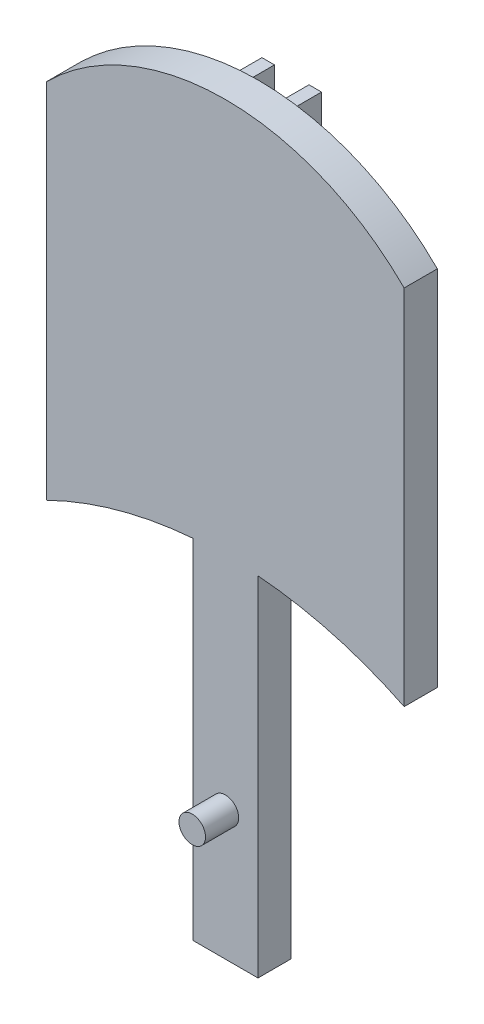
SolidWorks part; units mm, degrees
ref_plane "Front Plane" through (0, 0, 0) normal (0, 0, 1) x (1, 0, 0)
ref_plane "Top Plane" through (0, 0, 0) normal (0, 1, 0) x (1, 0, 0)
ref_plane "Right Plane" through (0, 0, 0) normal (1, 0, 0) x (0, 0, -1)
sketch "Sketch1" plane through (0, 0, 0) normal (0, 0, 1) x (1, 0, 0)
  line L1 (-17.1143, -17.3576) -> (17.1143, -17.3576)
  line L2 (-17.1143, -17.3576) -> (-17.1143, 17.3576)
  line L3 (-17.1143, 17.3576) -> (17.1143, 17.3576)
  line L4 (17.1143, -17.3576) -> (17.1143, 17.3576)
  line L5 (-17.1143, -17.3576) -> (17.1143, 17.3576) construction
  line L6 (-17.1143, 17.3576) -> (17.1143, -17.3576) construction
  arc A2 (-17.1143, 17.3576) -> (17.1143, 17.3576) centre (0, 0.1943) cw
  arc A3 (-17.1143, -17.3576) -> (17.1143, -17.3576) centre (0, -52.2147) cw
  point P0 (0, 0)
extrude "Boss-Extrude1" add sketch "Sketch1" along normal blind 3.175 contours A2 L3 | L2 A3 L4 L3
sketch "Sketch2" plane through (0, 0, 0) normal (0, 0, -1) x (-1, 0, 0)
  line L0 (1.6513, 22.2683) -> (1.6513, 23.2984)
  line L1 (-1.6513, -22.2683) -> (1.6513, -22.2683)
  line L2 (-1.6513, -22.2683) -> (-1.6513, 22.2683)
  line L3 (-1.6513, 22.2683) -> (1.6513, 22.2683)
  line L4 (1.6513, -22.2683) -> (1.6513, 22.2683)
  line L5 (-1.6513, -22.2683) -> (1.6513, 22.2683) construction
  line L6 (-1.6513, 22.2683) -> (1.6513, -22.2683) construction
  line L7 (-2.8534, -23.2984) -> (2.8534, -23.2984)
  line L8 (-2.8534, -23.2984) -> (-2.8534, 23.2984)
  line L9 (-2.8534, 23.2984) -> (2.8534, 23.2984)
  line L10 (2.8534, -23.2984) -> (2.8534, 23.2984)
  line L11 (-2.8534, -23.2984) -> (2.8534, 23.2984) construction
  line L12 (-2.8534, 23.2984) -> (2.8534, -23.2984) construction
  line L13 (-1.6513, 22.2683) -> (-1.6513, 23.2984)
  arc A0 (17.1143, -17.3576) -> (-17.1143, -17.3576) centre (0, -52.2147) ccw construction
  arc A1 (17.1143, -17.3576) -> (-17.1143, -17.3576) centre (0, -52.2147) ccw
  point P0 (0, 0)
  point P5 (0, 0)
  arc M3 (-17.1143, -17.3576) -> (17.1143, -17.3576) centre (0, -52.2147) cw
extrude "Boss-Extrude2" add sketch "Sketch2" along normal blind 3.175 contours L2 L13 L9 L8 M3 | L10 L9 L0 L4 M3
sketch "Sketch3" plane through (0, 0, 3.175) normal (0, 0, 1) x (1, 0, 0)
  line L0 (-3.1185, 0.3389) -> (3.1185, 0.3389)
  line L2 (-3.1185, 0.3389) -> (-3.1185, -46.8558)
  line L3 (-3.1185, -46.8558) -> (3.1185, -46.8558)
  line L4 (3.1185, 0.3389) -> (3.1185, -46.8558)
  line L5 (-0.0226, 0.3389) -> (3.1185, -46.8558) construction
  line L6 (-3.1185, -46.8558) -> (0.0226, 0.3389) construction
  point P0 (0, 0)
extrude "Boss-Extrude3" add sketch "Sketch3" against normal blind 3.175
sketch "Sketch4" plane through (0, 0, 3.175) normal (0, 0, 1) x (1, 0, 0)
  line L0 (0, -46.8558) -> (0, -34.5037)
  line L1 (-3.1185, -46.8558) -> (3.1185, -46.8558) construction
  circle A0 centre (0, -34.5037) radius 1.27
  dimension "D1" = 2.54
extrude "Boss-Extrude4" add sketch "Sketch4" along normal blind 3.175
sketch "Sketch5" plane through (0, 0, 6.35) normal (0, 0, 1) x (1, 0, 0)
  point P0 (0, -34.5037)
